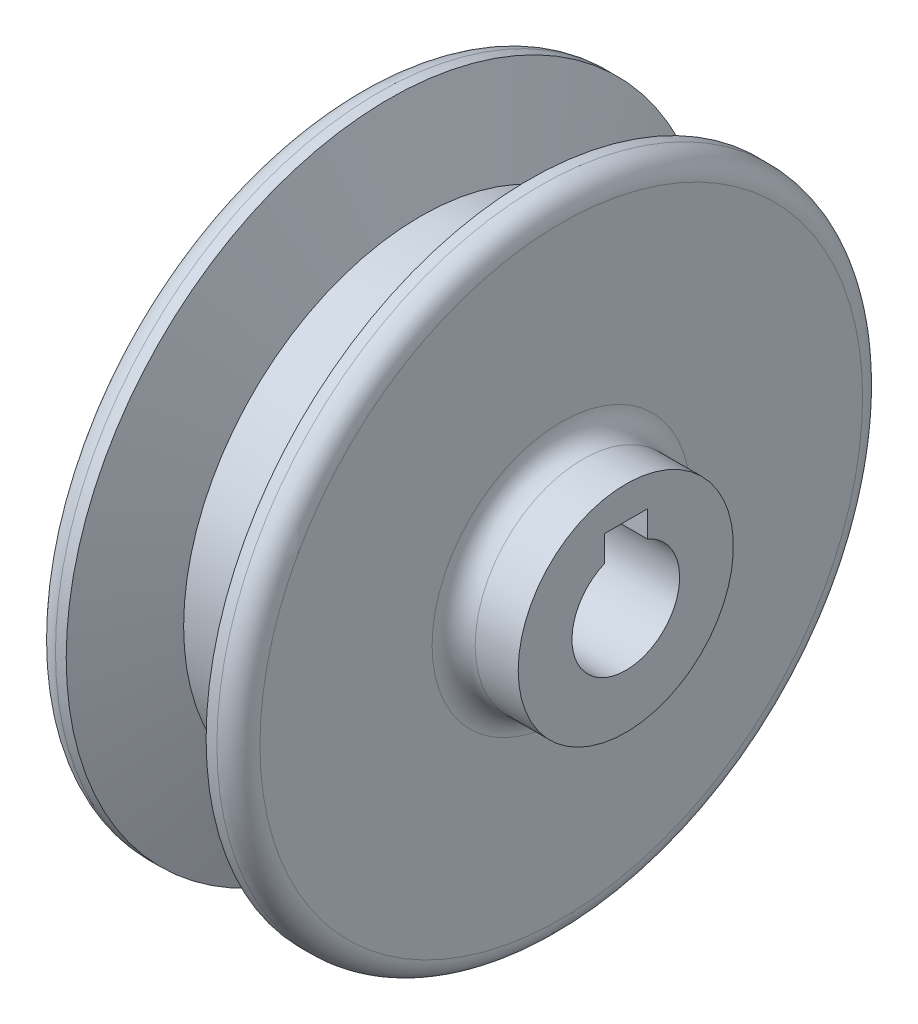
SolidWorks part; units mm, degrees
ref_plane "Front Plane" through (0, 0, 0) normal (0, 0, 1) x (1, 0, 0)
ref_plane "Top Plane" through (0, 0, 0) normal (0, 1, 0) x (1, 0, 0)
ref_plane "Right Plane" through (0, 0, 0) normal (1, 0, 0) x (0, 0, -1)
sketch "Sketch1" plane through (0, 0, 0) normal (0, 0, 1) x (1, 0, 0)
  line L0 (-3.7824, 0) -> (35.3318, 0) construction
  line L1 (16, 30) -> (17, 30)
  line L2 (0, 5) -> (0, 28)
  line L3 (2, 30) -> (3, 30)
  line L4 (25, 5) -> (25, 10)
  line L5 (5.9118, 22) -> (13.0882, 22)
  line L7 (0, 5) -> (25, 5)
  line L8 (19, 28) -> (19, 12)
  line L9 (21, 10) -> (25, 10)
  line L10 (3, 30) -> (5.9118, 22)
  line L11 (16, 30) -> (13.0882, 22)
  arc A0 (19, 12) -> (21, 10) centre (21, 12) ccw
  arc A1 (19, 28) -> (17, 30) centre (17, 28) ccw
  arc A2 (0, 28) -> (2, 30) centre (2, 28) cw
  dimension "D1" = 2
  dimension "D2" = 8.5134
  dimension "D3" = 7.1765
  dimension "D4" = 8.5134
  dimension "D5" = 110
  dimension "D6" = 5
  dimension "D7" = 1
  dimension "D8" = 1
  dimension "D9" = 30
  dimension "D10" = 5
  dimension "D11" = 4
revolve "Revolve1" add sketch "Sketch1" angle 360 about L0
sketch "Sketch2" plane through (25, 0, 0) normal (1, 0, 0) x (0, 0, -1)
  line L0 (-2, 0) -> (2, 0)
  line L1 (-2, 7) -> (2, 7)
  line L2 (-2, 7) -> (-2, 0)
  line L4 (2, 7) -> (2, 0)
  line L5 (-2, 7) -> (0, 0) construction
  line L6 (0, 0) -> (2, 7) construction
  point P0 (0, 0)
  dimension "D1" = 4
extrude "Cut-Extrude1" cut sketch "Sketch2" against normal blind 40
